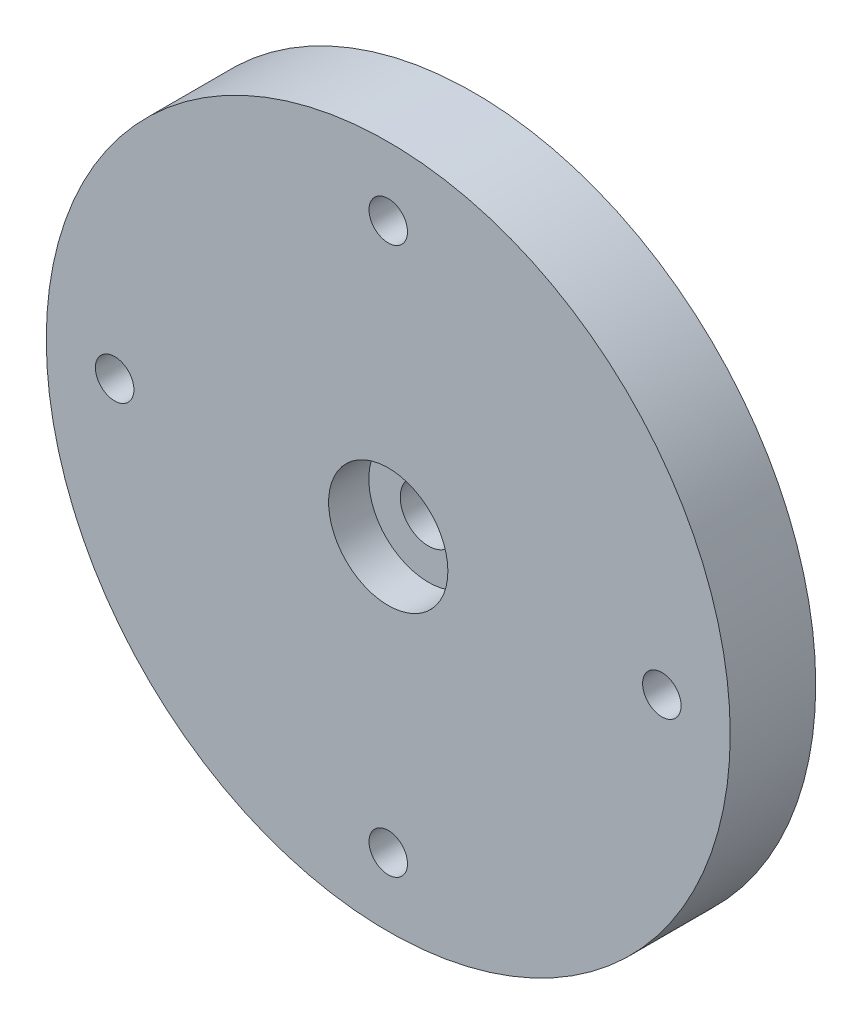
SolidWorks part; units mm, degrees
material "6061 Alloy"
ref_plane "Front Plane" through (0, 0, 0) normal (0, 0, 1) x (1, 0, 0)
ref_plane "Top Plane" through (0, 0, 0) normal (0, 1, 0) x (1, 0, 0)
ref_plane "Right Plane" through (0, 0, 0) normal (1, 0, 0) x (0, 0, -1)
sketch "Sketch1" plane through (0, 0, 0) normal (0, 0, 1) x (1, 0, 0)
  circle A0 centre (0, 0) radius 40
  dimension "D1" = 80
extrude "Boss-Extrude1" add sketch "Sketch1" along normal blind 10
hole_wizard "CBORE for M6 Hex Head Machine Screw1" positions "Sketch2" profile "Sketch3" counterbore size "M6" standard "ANSI Metric" end condition through all
sketch "Sketch2" plane through (0, 0, 10) normal (0, 0, 1) x (1, 0, 0)
  point P0 (0, 0)
sketch "Sketch3" plane through (0, 0, 10) normal (1, 0, 0) x (0, -1, 0)
  line L0 (0, 0) -> (0, 10)
  line L1 (0, 10) -> (3.3, 10)
  line L3 (3.3, 10) -> (3.3, 4.7)
  line L4 (3.3, 4.7) -> (6.975, 4.7)
  line L5 (6.975, 4.7) -> (6.975, 0)
  line L7 (6.975, 0) -> (0, 0)
  line L11 (0, -6.35) -> (0, 107.95) construction
  dimension "Thru Hole Dia." = 6.6
  dimension "Thru Hole Depth" = 10
  dimension "C'Bore Dia." = 13.95
  dimension "C'Bore Depth" = 4.7
hole_wizard "M4 Clearance Hole1" positions "Sketch4" profile "Sketch5" hole size "M4" standard "ANSI Metric" end condition through all
sketch "Sketch4" plane through (0, 0, 10) normal (0, 0, 1) x (1, 0, 0)
  circle A0 centre (0, 0) radius 32
  point P0 (0, 32)
  point P2 (32, 0)
  point P4 (0, -32)
  point P6 (-32, 0)
  dimension "D1" = 64
sketch "Sketch5" plane through (0, 32, 10) normal (1, 0, 0) x (0, -1, 0)
  line L0 (0, 0) -> (0, 10)
  line L1 (0, 10) -> (2.25, 10)
  line L2 (2.25, 10) -> (2.25, 0)
  line L5 (2.25, 0) -> (0, 0)
  line L11 (0, -6.35) -> (0, 107.95) construction
  dimension "Thru Hole Dia." = 4.5
  dimension "Thru Hole Depth" = 10
sketch "Sketch6" plane through (0, 0, 0) normal (0, 0, -1) x (-1, 0, 0)
  circle A0 centre (0, 0) radius 8.5
  dimension "D1" = 17
extrude "Cut-Extrude1" cut sketch "Sketch6" against normal blind 2
